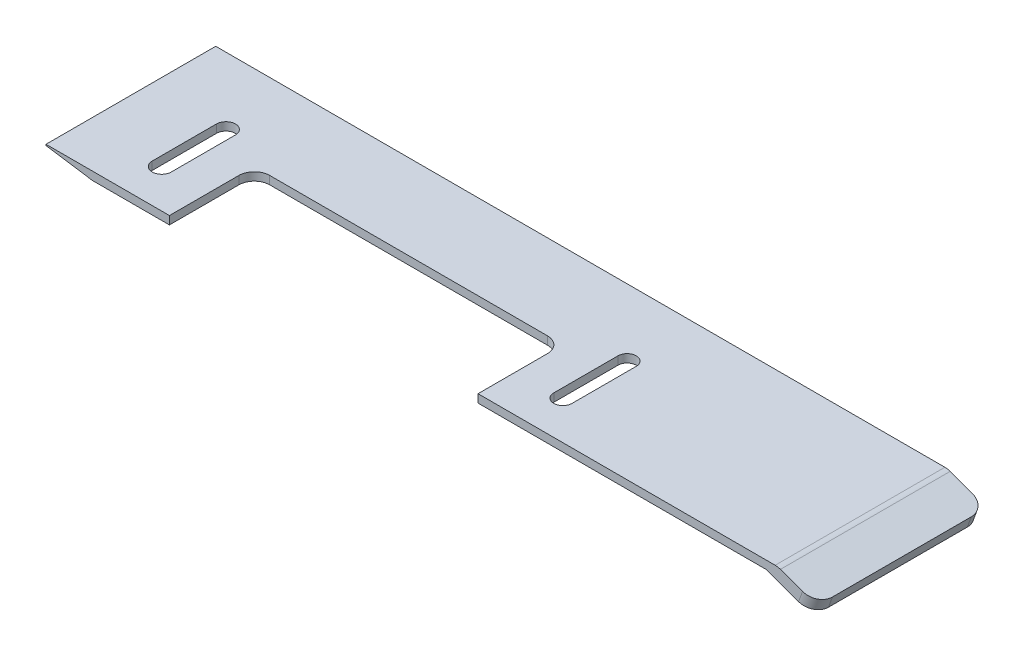
SolidWorks part; units mm, degrees
ref_plane "Front Plane" through (0, 0, 0) normal (0, 0, 1) x (1, 0, 0)
ref_plane "Top Plane" through (0, 0, 0) normal (0, 1, 0) x (1, 0, 0)
ref_plane "Right Plane" through (0, 0, 0) normal (1, 0, 0) x (0, 0, -1)
sketch "Sketch2" plane through (0, 0, 0) normal (0, 0, 1) x (1, 0, 0)
  line L0 (-70.922, 6.2188) -> (23.9466, 6.2188)
  line L1 (23.9466, 6.2188) -> (29.0209, 4.3719)
  line L2 (29.0209, 4.3719) -> (28.5079, 2.9624)
  line L3 (28.5079, 2.9624) -> (22.4676, 5.1608)
  line L4 (22.4676, 5.1608) -> (-64.922, 5.1608)
  line L5 (-64.922, 5.1608) -> (-70.922, 6.061)
  line L6 (-70.922, 6.061) -> (-70.922, 6.2188)
  dimension "D1" = 6
  dimension "D2" = 99.96
  dimension "D3" = 5.4
  dimension "D4" = 20
  dimension "D5" = 1.5
extrude "Boss-Extrude1" add sketch "Sketch2" along normal blind 22
fillet "Fillet10" radius 2 2 edges at (28.7644, 3.6671, 22) (28.7644, 3.6671, 0)
fillet "Fillet11" radius 2 1 edges at (23.9466, 6.2188, 11)
sketch "Sketch4" plane through (0, 5.1608, 0) normal (0, -1, 0) x (1, 0, 0)
  line L0 (-70.922, 22) -> (-70.922, 0) construction
  line L1 (-14.922, 29.4559) -> (-54.922, 29.4559)
  line L2 (-14.922, 29.4559) -> (-14.922, 11)
  line L3 (-14.922, 11) -> (-54.922, 11)
  line L4 (-54.922, 29.4559) -> (-54.922, 11)
  line L6 (-59.6886, 8.6742) -> (-59.6886, 17)
  line L8 (-62.1555, 8.6742) -> (-62.1555, 17)
  line L10 (-7.74, 8.6742) -> (-7.74, 17)
  line L12 (-10.1041, 8.6742) -> (-10.1041, 17)
  line L13 (-64.922, 0) -> (22.4676, 0) construction
  arc A0 (-59.6886, 17) -> (-62.1555, 17) centre (-60.922, 17) ccw
  arc A1 (-62.1555, 8.6742) -> (-59.6886, 8.6742) centre (-60.922, 8.6742) ccw
  arc A2 (-7.74, 17) -> (-10.1041, 17) centre (-8.922, 17) ccw
  arc A3 (-10.1041, 8.6742) -> (-7.74, 8.6742) centre (-8.922, 8.6742) ccw
  dimension "D1" = 16
  dimension "D2" = 56
  dimension "D3" = 17
  dimension "D4" = 17
  dimension "D5" = 11
extrude "Cut-Extrude1" cut sketch "Sketch4" against normal blind 30
fillet "Fillet12" radius 2 2 edges at (-14.922, 5.6898, 11) (-54.922, 5.6898, 11)
